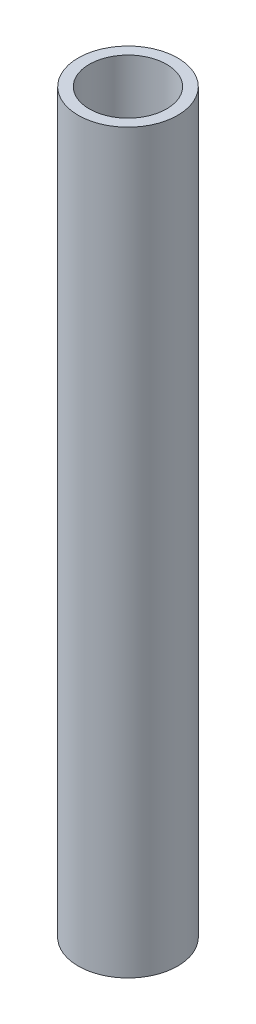
SolidWorks part; units mm, degrees
ref_plane "Front Plane" through (0, 0, 0) normal (0, 0, 1) x (1, 0, 0)
ref_plane "Top Plane" through (0, 0, 0) normal (0, 1, 0) x (1, 0, 0)
ref_plane "Right Plane" through (0, 0, 0) normal (1, 0, 0) x (0, 0, -1)
sketch "Sketch1" plane through (0, 0, 0) normal (0, 1, 0) x (1, 0, 0)
  circle A0 centre (0, 0) radius 13.5
  circle A1 centre (0, 0) radius 10.5
  dimension "D1" = 3
  dimension "D2" = 21
extrude "Boss-Extrude2" add sketch "Sketch1" along normal blind 200
sketch3d "3DSketch1" plane through (0, 0, 0) normal (0, 0, 1) x (1, 0, 0)
